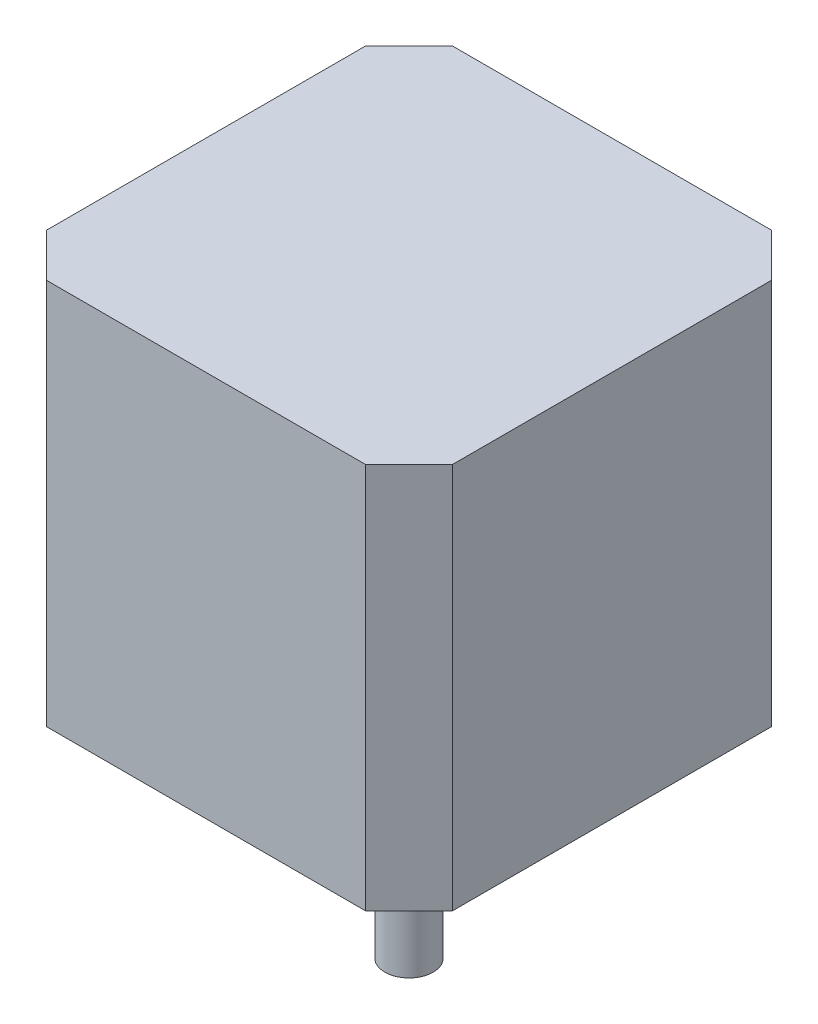
SolidWorks part; units mm, degrees
ref_plane "Front Plane" through (0, 0, 0) normal (0, 0, 1) x (1, 0, 0)
ref_plane "Top Plane" through (0, 0, 0) normal (0, 1, 0) x (1, 0, 0)
ref_plane "Right Plane" through (0, 0, 0) normal (1, 0, 0) x (0, 0, -1)
sketch "Sketch1" plane through (0, 0, 0) normal (0, 1, 0) x (1, 0, 0)
  line L0 (21, -21) -> (21, 21)
  line L1 (21, -21) -> (-21, -21)
  line L2 (21, 21) -> (-21, 21)
  line L3 (-21, -21) -> (-21, 21)
  line L4 (21, -21) -> (-21, 21) construction
  line L5 (21, 21) -> (-21, -21) construction
  point P1 (0, 0)
  dimension "D1" = 42
  dimension "D2" = 42
extrude "Boss-Extrude1" add sketch "Sketch1" along normal blind 40
sketch "Sketch2" plane through (0, 0, 0) normal (0, -1, 0) x (1, 0, 0)
  circle A0 centre (0, 0) radius 11
  dimension "D1" = 22
extrude "Boss-Extrude2" add sketch "Sketch2" along normal blind 2
sketch "Sketch3" plane through (0, -2, 0) normal (0, -1, 0) x (1, 0, 0)
  circle A0 centre (0, 0) radius 2.5
  dimension "D1" = 5
extrude "Boss-Extrude3" add sketch "Sketch3" along normal blind 21
chamfer "Chamfer1" distance 4.5 angle 45 4 edges at (21, 20, 21) (21, 20, -21) (-21, 20, -21) (-21, 20, 21)
sketch "Sketch4" plane through (0, 0, 0) normal (0, -1, 0) x (1, 0, 0)
  line L0 (15.5, -15.5) -> (-15.5, -15.5) construction
  line L1 (15.5, -15.5) -> (15.5, 15.5) construction
  line L2 (-15.5, -15.5) -> (-15.5, 15.5) construction
  line L3 (15.5, 15.5) -> (-15.5, 15.5) construction
  line L4 (15.5, -15.5) -> (-15.5, 15.5) construction
  line L5 (-15.5, -15.5) -> (15.5, 15.5) construction
  point P1 (0, 0)
  dimension "D1" = 31
  dimension "D2" = 31
hole_wizard "M3x0.5 Tapped Hole2" positions "Sketch8" profile "Sketch7" tap size "M3x0.5" standard "ANSI Metric"
sketch "Sketch8" plane through (0, 0, 0) normal (0, -1, 0) x (-1, 0, 0)
  point P0 (15.5, 15.5)
  point P3 (-15.5, 15.5)
  point P6 (-15.5, -15.5)
  point P9 (15.5, -15.5)
sketch "Sketch7" plane through (-15.5, 0, -15.5) normal (1, 0, 0) x (0, 0, -1)
  line L0 (0, 0) -> (0, 6.7511)
  line L1 (0, 6.7511) -> (1.25, 6)
  line L2 (1.25, 6) -> (1.25, 0)
  line L5 (1.25, 0) -> (0, 0)
  line L10 (0, 6.7511) -> (-1.25, 6) construction
  line L11 (0, -6.35) -> (0, 107.95) construction
  dimension "Tap Drill Dia." = 2.5
  dimension "Tap Drill Depth" = 6
  dimension "Drill Angle" = 118
cosmetic thread "Hole Thread5" parameters "D1"=4.5, "D2"=3
cosmetic thread "Hole Thread6" parameters "D1"=4.5, "D2"=3
cosmetic thread "Hole Thread7" parameters "D1"=4.5, "D2"=3
cosmetic thread "Hole Thread8" parameters "D1"=4.5, "D2"=3
